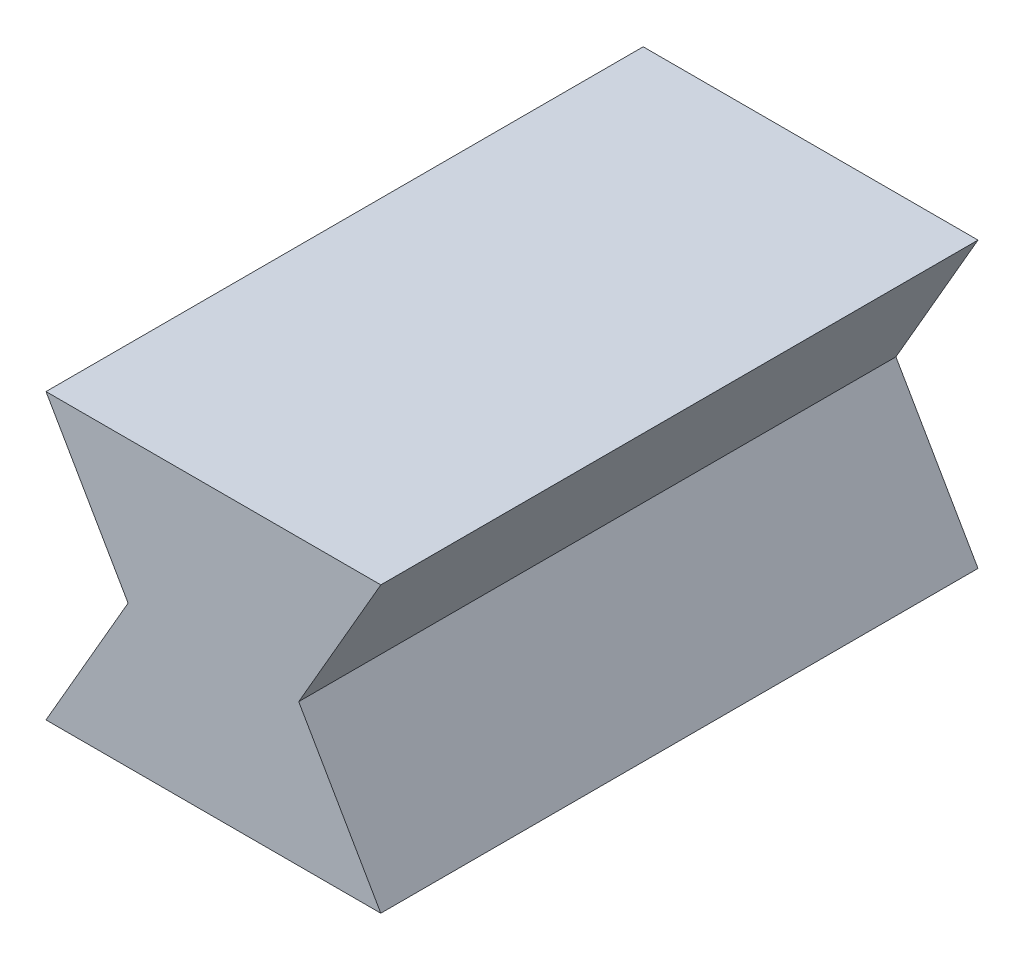
SolidWorks part; units mm, degrees
material "ABS"
ref_plane "Front Plane" through (0, 0, 0) normal (0, 0, 1) x (1, 0, 0)
ref_plane "Top Plane" through (0, 0, 0) normal (0, 1, 0) x (1, 0, 0)
ref_plane "Right Plane" through (0, 0, 0) normal (1, 0, 0) x (0, 0, -1)
sketch "Sketch1" plane through (0, 0, 0) normal (0, 0, 1) x (1, 0, 0)
  line L0 (-3, 0) -> (3, 0)
  line L1 (3, 0) -> (5.8868, -5)
  line L2 (5.8868, -5) -> (-5.8868, -5)
  line L3 (-5.8868, -5) -> (-3, 0)
  line L8 (5.8868, 5) -> (-5.8868, 5)
  line L9 (3, 0) -> (5.8868, 5)
  line L10 (-5.8868, 5) -> (-3, 0)
  point P3 (0, 0)
  point P6 (0, -5)
  dimension "D1" = 60
  dimension "D2" = 6
  dimension "D3" = 5
extrude "Extrude2" add sketch "Sketch1" along normal mid plane 21
